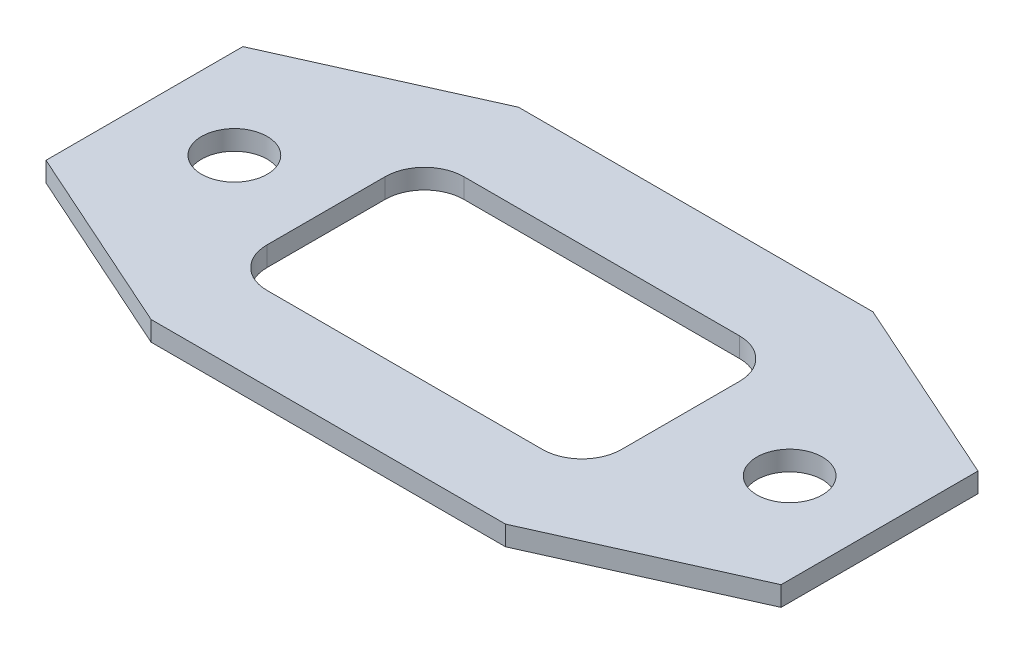
SolidWorks part; units mm, degrees
ref_plane "Front Plane" through (0, 0, 0) normal (0, 0, 1) x (1, 0, 0)
ref_plane "Top Plane" through (0, 0, 0) normal (0, 1, 0) x (1, 0, 0)
ref_plane "Right Plane" through (0, 0, 0) normal (1, 0, 0) x (0, 0, -1)
sketch "Sketch1" plane through (0, 0, 0) normal (0, 1, 0) x (1, 0, 0)
  line L0 (13, 4.3337) -> (13, -4.6663)
  line L1 (-11, 7.3337) -> (10, 7.3337)
  line L2 (-14, -4.6663) -> (-14, 4.3337)
  line L3 (10, -7.6663) -> (-11, -7.6663)
  line L4 (-13.5, 14) -> (13.5, 14)
  line L5 (28, 7.5) -> (-28, 7.5) construction
  line L6 (13.5, 14) -> (28, 7.5)
  line L7 (28, 7.5) -> (28, -7.5)
  line L8 (-28, 7.5) -> (-28, -7.5)
  line L9 (0, -7.5) -> (0, 7.5) construction
  line L10 (-13.5, 14) -> (-28, 7.5)
  line L11 (13.5, 0) -> (-13.5, 0) construction
  line L12 (13.5, -14) -> (28, -7.5)
  line L13 (-13.5, -14) -> (13.5, -14)
  line L14 (-13.5, -14) -> (-28, -7.5)
  arc A0 (13, 4.3337) -> (10, 7.3337) centre (10, 4.3337) ccw
  arc A1 (-11, 7.3337) -> (-14, 4.3337) centre (-11, 4.3337) ccw
  arc A2 (-14, -4.6663) -> (-11, -7.6663) centre (-11, -4.6663) ccw
  arc A3 (10, -7.6663) -> (13, -4.6663) centre (10, -4.6663) ccw
  circle A4 centre (21.15, 0) radius 2.5
  circle A5 centre (-21.15, 0) radius 2.5
  point P27 (28, 0)
  point P28 (-28, 0)
  dimension "D4" = 5
  dimension "D6" = 3
  dimension "D1" = 27
  dimension "D2" = 56
  dimension "D3" = 15
  dimension "D5" = 21
  dimension "D7" = 14.5
  dimension "D8" = 13
  dimension "D9" = 21.15
  dimension "D10" = 7.3337
  dimension "D11" = 21.15
  dimension "D12" = 14
  dimension "D13" = 7.6663
extrude "Boss-Extrude1" add sketch "Sketch1" along normal blind 1.5
